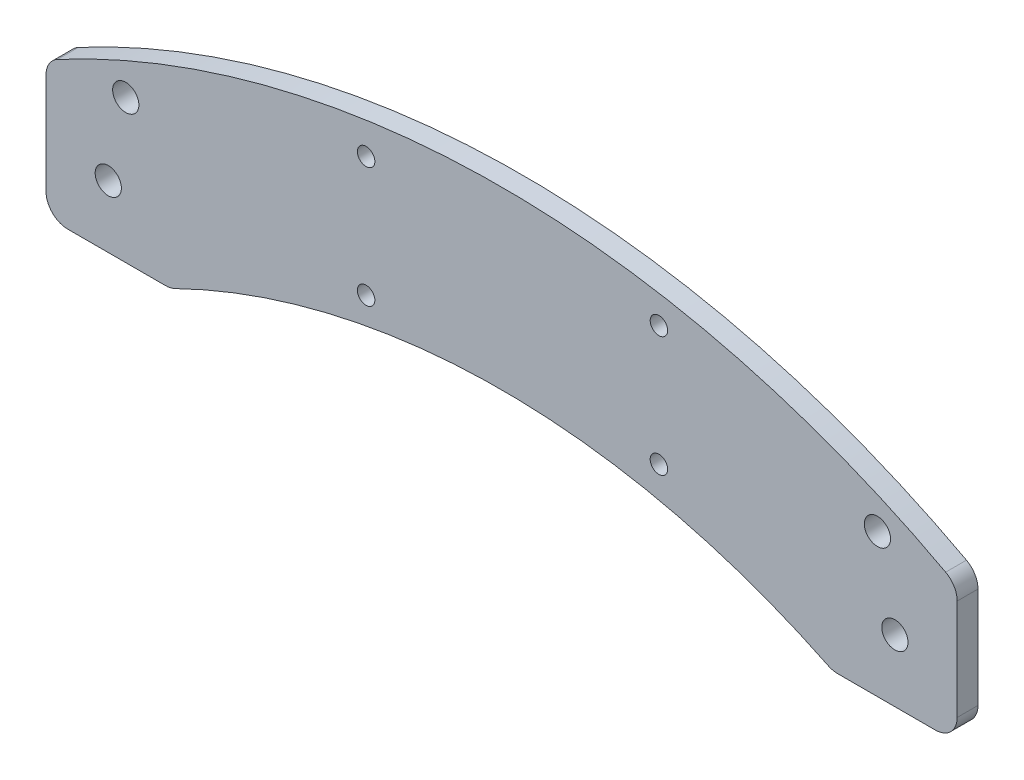
SolidWorks part; units mm, degrees
ref_plane "Front Plane" through (0, 0, 0) normal (0, 0, 1) x (1, 0, 0)
ref_plane "Top Plane" through (0, 0, 0) normal (0, 1, 0) x (1, 0, 0)
ref_plane "Right Plane" through (0, 0, 0) normal (1, 0, 0) x (0, 0, -1)
sketch "Sketch1" plane through (0, 0, 0) normal (0, 0, 1) x (1, 0, 0)
  line L0 (-14.25, -9.25) -> (-14.25, 13.816)
  line L4 (194.25, 13.816) -> (194.25, -9.25)
  line L5 (189.25, -14.25) -> (166.9166, -14.25)
  line L9 (13.0834, -14.25) -> (-9.25, -14.25)
  line L10 (14.25, -30) -> (14.25, 6.9138) construction
  line L11 (194.25, 14.25) -> (194.25, -14.25) construction
  line L12 (194.25, -14.25) -> (185.75, -30) construction
  line L13 (165.75, -30) -> (165.75, 6.9138) construction
  circle A0 centre (59, 34.2905) radius 2
  circle A1 centre (59, 6.7905) radius 2
  circle A2 centre (126, 34.2905) radius 2
  circle A3 centre (126, 6.7905) radius 2
  circle A4 centre (180, 0) radius 3
  circle A5 centre (0, 0) radius 3
  arc A6 (164.7189, -13.7412) -> (15.2811, -13.7412) centre (90, -166.4405) ccw
  arc A7 (-11.6131, 18.2224) -> (191.6131, 18.2224) centre (90, -171.25) cw
  circle A8 centre (4, 18.5) radius 3
  circle A9 centre (176, 18.5) radius 3
  arc A10 (194.25, -9.25) -> (189.25, -14.25) centre (189.25, -9.25) cw
  arc A11 (-14.25, -9.25) -> (-9.25, -14.25) centre (-9.25, -9.25) ccw
  arc A12 (166.9166, -14.25) -> (164.7189, -13.7412) centre (166.9166, -9.25) cw
  arc A13 (15.2811, -13.7412) -> (13.0834, -14.25) centre (13.0834, -9.25) cw
  arc A14 (191.6131, 18.2224) -> (194.25, 13.816) centre (189.25, 13.816) cw
  arc A15 (-14.25, 13.816) -> (-11.6131, 18.2224) centre (-9.25, 13.816) cw
  point P56 (194.25, -14.25)
  point P59 (-14.25, -14.25)
  point P62 (165.75, -14.25)
  point P65 (14.25, -14.25)
  dimension "D1" = 6
  dimension "D2" = 4
  dimension "D3" = 170
  dimension "D4" = 58
  dimension "D5" = 6
  dimension "D6" = 215
  dimension "D7" = 5
  dimension "D8" = 5
  dimension "D9" = 5
  dimension "D10" = 5
extrude "Boss-Extrude1" add sketch "Sketch1" along normal blind 4.7625
sketch "Sketch3" plane through (0, 0, 4.7625) normal (0, 0, 1) x (1, 0, 0)
  line L0 (11.2433, 14.1454) -> (7.8129, -1.7204)
  line L1 (53, 28.3797) -> (53, 16.5616)
  line L2 (132, 27.262) -> (132, 16.2278)
  line L3 (168.8769, 13.5895) -> (172.1871, -1.7204)
  line L4 (13.1841, 23.1216) -> (53, 5.6264) construction
  line L5 (166.8159, 23.1216) -> (132, 4.4747) construction
  line L6 (157.1367, 21.3408) -> (139.3607, 11.8202)
  line L7 (142.7298, 6.8183) -> (161.6291, 16.9405)
  line L8 (40.3208, 7.9208) -> (18.1418, 17.6663)
  line L9 (24.1265, 21.5903) -> (45.9886, 11.9841)
  line L10 (120, 31.2123) -> (120, 12.8247)
  line L11 (65, 31.7672) -> (65, 13.4512)
  arc A0 (161.6291, 16.9405) -> (168.8769, 13.5895) centre (163.9898, 12.5328) cw
  arc A1 (132, 27.262) -> (138.152, 32.1275) centre (137, 27.262) cw
  arc A2 (167.3561, -8.3518) -> (12.6439, -8.3518) centre (90, -166.4405) ccw
  arc A3 (165.1647, -7.2982) -> (143.2387, 1.3142) centre (90, -166.4405) ccw
  circle A4 centre (4, 18.5) radius 3 construction
  arc A5 (188.7774, 12.9348) -> (-8.7774, 12.9348) centre (90, -171.25) ccw
  arc A6 (156.6774, 26.8286) -> (138.152, 32.1275) centre (90, -171.25) ccw
  circle A7 centre (0, 0) radius 3 construction
  circle A8 centre (180, 0) radius 3 construction
  circle A9 centre (176, 18.5) radius 3 construction
  circle A10 centre (126, 34.2905) radius 2 construction
  circle A11 centre (59, 34.2905) radius 2 construction
  arc A12 (115.6127, 36.1747) -> (69.5098, 36.7432) centre (90, -171.25) ccw
  arc A13 (114.3094, 7.8726) -> (70.5525, 8.4818) centre (90, -166.4405) ccw
  arc A14 (132, 16.2278) -> (139.3607, 11.8202) centre (137, 16.2278) ccw
  arc A15 (53, 28.3797) -> (46.9706, 33.2725) centre (48, 28.3797) ccw
  arc A16 (53, 16.5616) -> (45.9886, 11.9841) centre (48, 16.5616) cw
  arc A17 (18.1418, 17.6663) -> (11.2433, 14.1454) centre (16.1304, 13.0888) ccw
  arc A18 (157.1367, 21.3408) -> (156.6774, 26.8286) centre (155.7203, 23.9853) ccw
  arc A19 (142.7298, 6.8183) -> (143.2387, 1.3142) centre (144.1462, 4.1737) ccw
  arc A20 (40.3208, 7.9208) -> (39.9668, 2.298) centre (39.114, 5.1743) cw
  arc A21 (24.1265, 21.5903) -> (24.3916, 27.1852) centre (25.3334, 24.3369) cw
  arc A22 (165.1647, -7.2982) -> (172.1871, -1.7204) centre (167.3, -2.7771) ccw
  arc A23 (14.8353, -7.2982) -> (7.8129, -1.7204) centre (12.7, -2.7771) cw
  arc A24 (39.9668, 2.298) -> (14.8353, -7.2982) centre (90, -166.4405) ccw
  arc A25 (46.9706, 33.2725) -> (24.3916, 27.1852) centre (90, -171.25) ccw
  arc A26 (69.5098, 36.7432) -> (65, 31.7672) centre (70, 31.7672) ccw
  arc A27 (115.6127, 36.1747) -> (120, 31.2123) centre (115, 31.2123) cw
  arc A28 (114.3094, 7.8726) -> (120, 12.8247) centre (115, 12.8247) ccw
  arc A29 (70.5525, 8.4818) -> (65, 13.4512) centre (70, 13.4512) cw
  point P46 (53, 34.4488)
  dimension "D6" = 8
  dimension "D8" = 6
  dimension "D13" = 5
  dimension "D14" = 3
  dimension "D15" = 5
  dimension "D17" = 6
  dimension "D18" = 5
  dimension "D3" = 8
  dimension "D4" = 8
  dimension "D5" = 8
  dimension "D7" = 6
  dimension "D9" = 3
  dimension "D10" = 6
  dimension "D11" = 3
  dimension "D12" = 6
  dimension "D16" = 6
  dimension "D1" = 6
  dimension "D2" = 6
extrude "Cut-Extrude1" [suppressed] cut sketch "Sketch3" against normal offset from surface (4.35 mm away) 2
